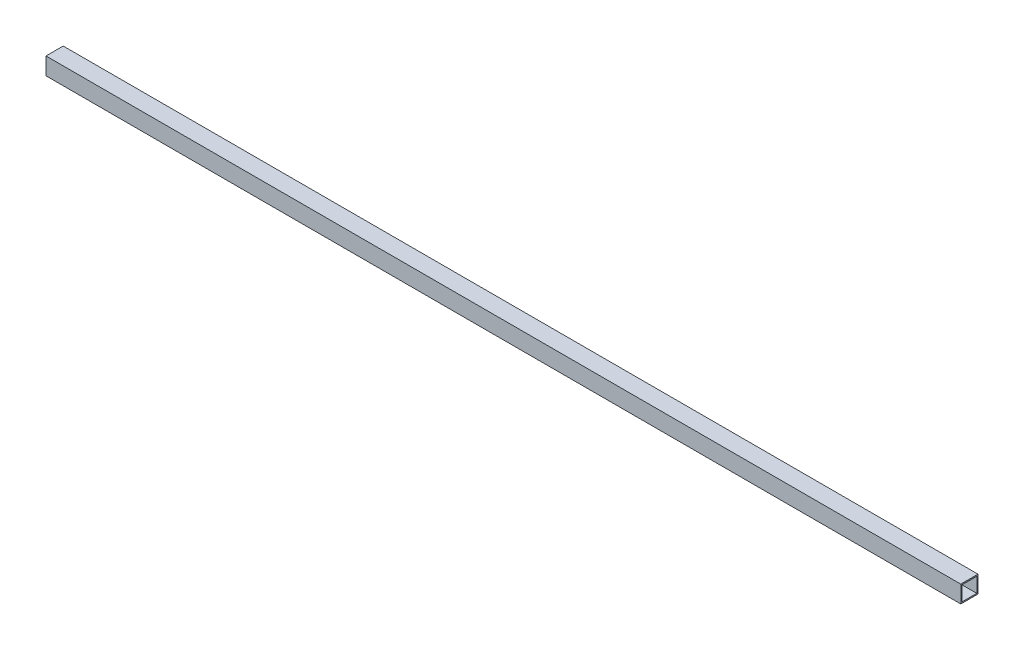
SolidWorks part; units mm, degrees
ref_plane "Front Plane" through (0, 0, 0) normal (0, 0, 1) x (1, 0, 0)
ref_plane "Top Plane" through (0, 0, 0) normal (0, 1, 0) x (1, 0, 0)
ref_plane "Right Plane" through (0, 0, 0) normal (1, 0, 0) x (0, 0, -1)
sketch "Sketch1" plane through (0, 0, 0) normal (0, 0, 1) x (1, 0, 0)
  line L1 (0, 0) -> (2360.422, 0)
  line L2 (0, 0) -> (0, 44.45)
  line L3 (0, 44.45) -> (2360.422, 44.45)
  line L4 (2360.422, 0) -> (2360.422, 44.45)
  dimension "D1" = 2360.422
  dimension "D2" = 44.45
extrude "Boss-Extrude1" add sketch "Sketch1" along normal blind 44.45
shell "Shell1" thickness 3.175
